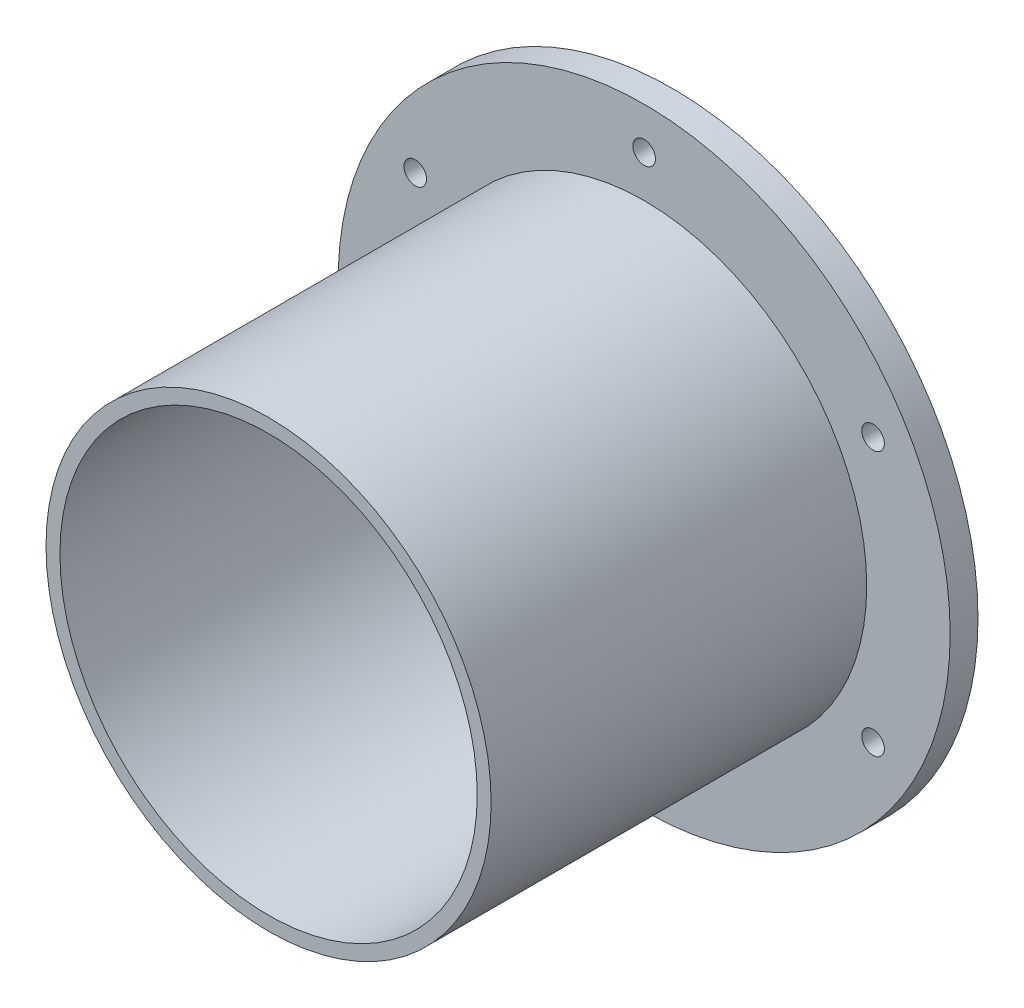
SolidWorks part; units mm, degrees
ref_plane "Front Plane" through (0, 0, 0) normal (0, 0, 1) x (1, 0, 0)
ref_plane "Top Plane" through (0, 0, 0) normal (0, 1, 0) x (1, 0, 0)
ref_plane "Right Plane" through (0, 0, 0) normal (1, 0, 0) x (0, 0, -1)
sketch "Sketch1" plane through (0, 0, 0) normal (0, 0, 1) x (1, 0, 0)
  circle A0 centre (0, 0) radius 69.85
  circle A1 centre (0, 0) radius 50.8
  circle A2 centre (0, 60.325) radius 2.5794
  circle A3 centre (-52.243, 30.1625) radius 2.5794
  circle A4 centre (-52.243, -30.1625) radius 2.5794
  circle A5 centre (0, -60.325) radius 2.5794
  circle A6 centre (52.243, -30.1625) radius 2.5794
  circle A7 centre (52.243, 30.1625) radius 2.5794
extrude "Extrude1" add sketch "Sketch1" along normal blind 6.35
sketch "Sketch2" plane through (0, 0, 0) normal (0, 0, 1) x (1, 0, 0)
  circle A0 centre (0, 0) radius 47.625
  circle A1 centre (0, 0) radius 50.8
extrude "Extrude2" add sketch "Sketch2" along normal blind 92.075
